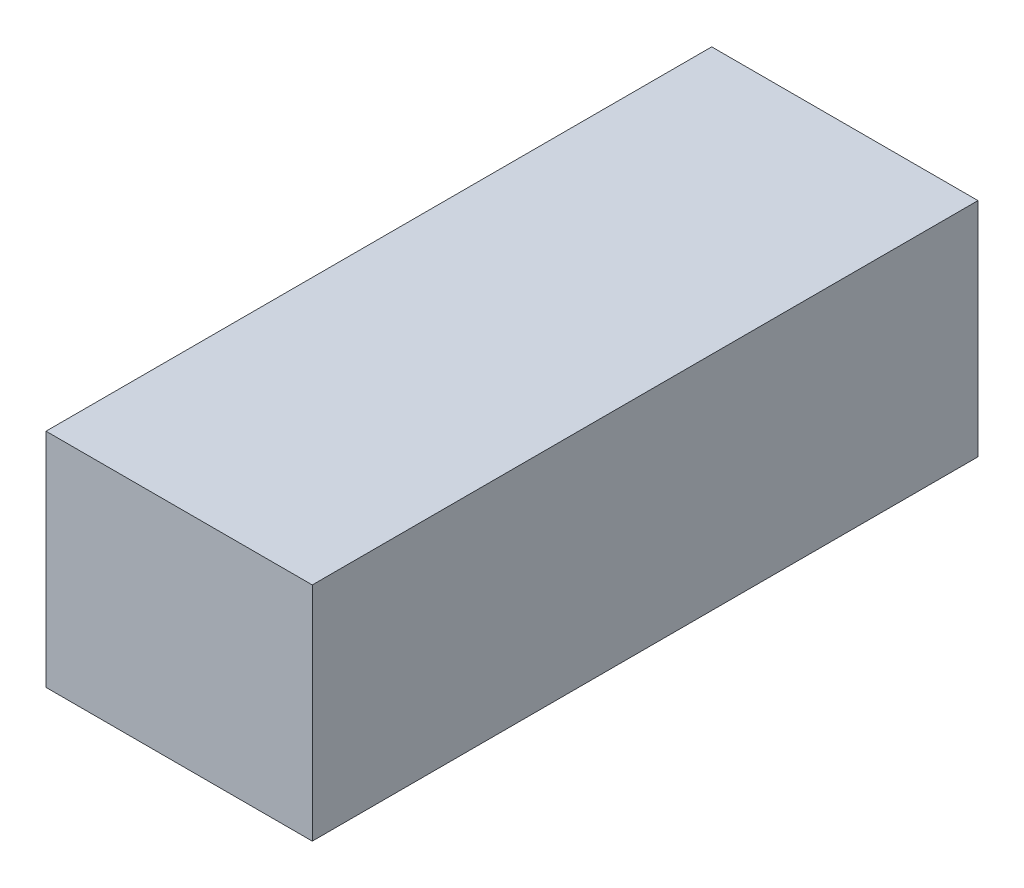
SolidWorks part; units mm, degrees
ref_plane "Płaszczyzna przednia" through (0, 0, 0) normal (0, 0, 1) x (1, 0, 0)
ref_plane "Płaszczyzna górna" through (0, 0, 0) normal (0, 1, 0) x (1, 0, 0)
ref_plane "Płaszczyzna prawa" through (0, 0, 0) normal (1, 0, 0) x (0, 0, -1)
sketch "Sketch1" plane through (0, 0, 0) normal (0, 1, 0) x (1, 0, 0)
  line L1 (-1.6694, -22.5) -> (16.3306, -22.5)
  line L2 (-1.6694, -22.5) -> (-1.6694, 22.5)
  line L3 (-1.6694, 22.5) -> (16.3306, 22.5)
  line L4 (16.3306, -22.5) -> (16.3306, 22.5)
  dimension "D1" = 45
  dimension "D2" = 18
extrude "Boss-Extrude1" add sketch "Sketch1" along normal blind 15
